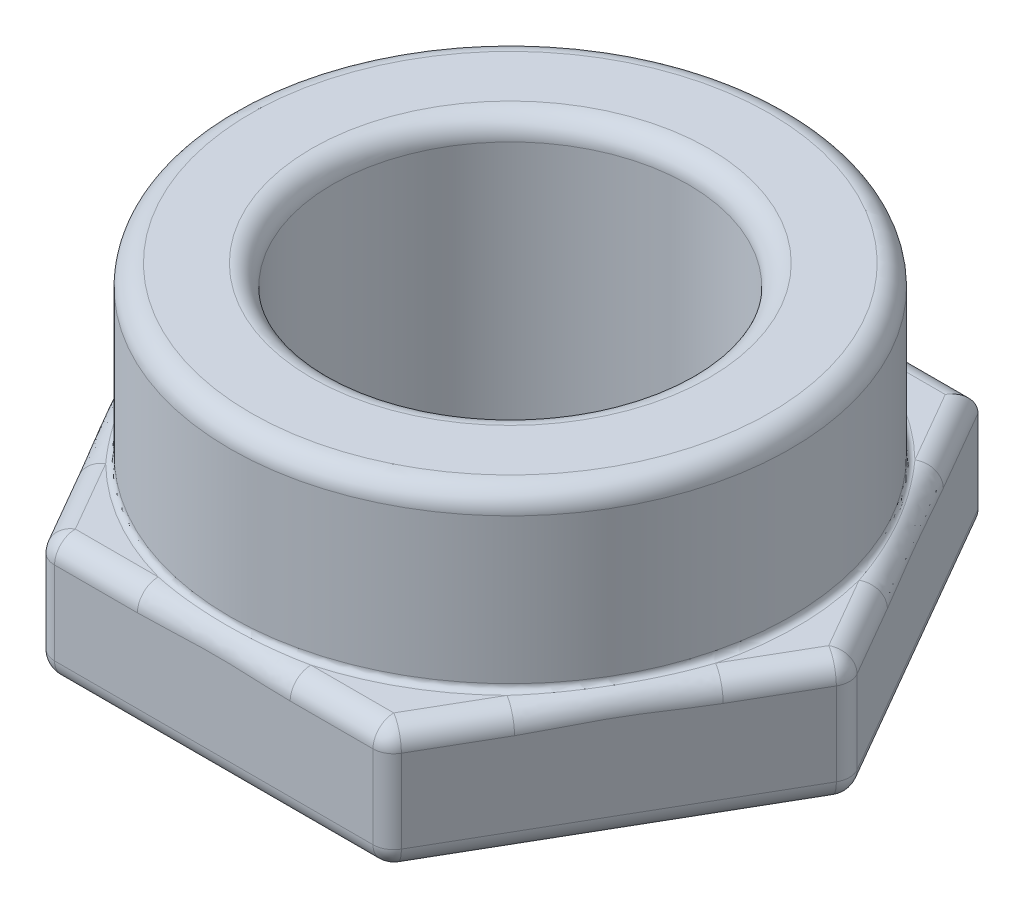
SolidWorks part; units mm, degrees
ref_plane "Front Plane" through (0, 0, 0) normal (0, 0, 1) x (1, 0, 0)
ref_plane "Top Plane" through (0, 0, 0) normal (0, 1, 0) x (1, 0, 0)
ref_plane "Right Plane" through (0, 0, 0) normal (1, 0, 0) x (0, 0, -1)
sketch "Sketch1" plane through (0, 0, 0) normal (0, 1, 0) x (1, 0, 0)
  line L1 (29.3294, 0) -> (14.6647, 25.4)
  line L2 (14.6647, 25.4) -> (-14.6647, 25.4)
  line L3 (-14.6647, 25.4) -> (-29.3294, 0)
  line L4 (-29.3294, 0) -> (-14.6647, -25.4)
  line L5 (-14.6647, -25.4) -> (14.6647, -25.4)
  line L6 (14.6647, -25.4) -> (29.3294, 0)
  circle A0 centre (0, 0) radius 25.4 construction
  dimension "D1" = 50.8
extrude "Boss-Extrude1" add sketch "Sketch1" along normal blind 10.668
sketch "Sketch2" plane through (0, 10.668, 0) normal (0, 1, 0) x (1, 0, 0)
  circle A0 centre (0, 0) radius 24.003
  dimension "D1" = 48.006
extrude "Boss-Extrude2" add sketch "Sketch2" along normal blind 14.732
sketch "Sketch3" plane through (0, 25.4, 0) normal (0, 1, 0) x (1, 0, 0)
  circle A0 centre (0, 0) radius 15.24
  dimension "D1" = 30.48
extrude "Cut-Extrude1" cut sketch "Sketch3" against normal through all
fillet "Fillet2" radius 0.508 1 edges at (0, 10.668, 24.003)
fillet "Fillet1" radius 1.778 20 edges at (-29.3294, 5.334, 0) (-21.997, 10.668, 12.7) (-21.997, 0, 12.7) (-14.6647, 5.334, 25.4) (0, 10.668, 25.4) (14.6647, 5.334, 25.4) (0, 0, 25.4) (0, 0, 15.24) (0, 0, -25.4) (-21.997, 0, -12.7) (-21.997, 10.668, -12.7) (-14.6647, 5.334, -25.4) (0, 10.668, -25.4) (29.3294, 5.334, 0) (21.997, 10.668, -12.7) (21.997, 0, -12.7) (21.997, 10.668, 12.7) (21.997, 0, 12.7) (0, 25.4, 15.24) (0, 25.4, 24.003)
